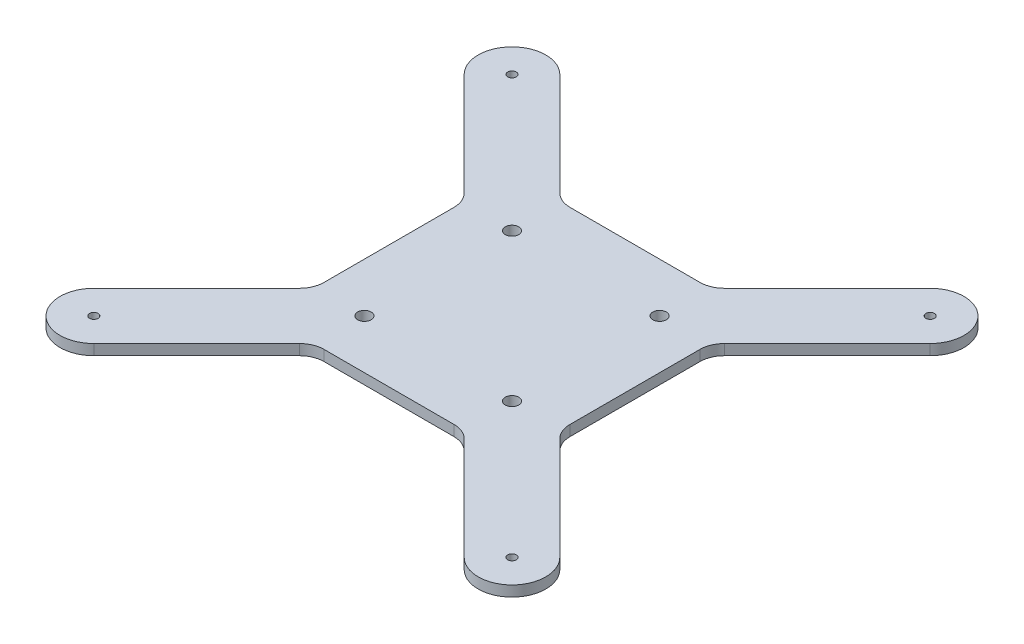
SolidWorks part; units mm, degrees
ref_plane "Front Plane" through (0, 0, 0) normal (0, 0, 1) x (1, 0, 0)
ref_plane "Top Plane" through (0, 0, 0) normal (0, 1, 0) x (1, 0, 0)
ref_plane "Right Plane" through (0, 0, 0) normal (1, 0, 0) x (0, 0, -1)
sketch "Sketch1" plane through (0, 0, 0) normal (0, 1, 0) x (1, 0, 0)
  line L0 (50, 100) -> (50, 0) construction
  line L1 (0, 0) -> (100, 0)
  line L2 (0, 0) -> (0, 100)
  line L3 (0, 100) -> (100, 100)
  line L4 (100, 0) -> (100, 100)
  line L5 (0, 50) -> (100, 50) construction
  circle A0 centre (20, 80) radius 2.75
  circle A1 centre (80, 80) radius 2.75
  circle A2 centre (80, 20) radius 2.75
  circle A3 centre (20, 20) radius 2.75
  circle A14 centre (50, 50) radius 7.5 construction
  point P54 (50, 50)
  dimension "D4" = 5.5
  dimension "D11" = 15
  dimension "D1" = 100
  dimension "D2" = 60
  dimension "D3" = 60
extrude "Boss-Extrude1" add sketch "Sketch1" along normal blind 4.3
sketch "Sketch2" plane through (0, 4.3, 0) normal (0, 1, 0) x (1, 0, 0)
  line L0 (50, 100) -> (50, 0) construction
  line L1 (100, 100) -> (0, 100) construction
  line L2 (0, 0) -> (100, 0) construction
  line L3 (0, 50) -> (100, 50) construction
  line L4 (0, 100) -> (0, 0) construction
  line L5 (100, 0) -> (100, 100) construction
  line L6 (0, 80.5546) -> (-44.7227, 125.2773)
  line L7 (-25.2773, 144.7227) -> (19.4454, 100)
  line L8 (0, 80.5546) -> (0, 100)
  line L9 (0, 100) -> (19.4454, 100)
  line L10 (100, 100) -> (100, 80.5546)
  line L11 (144.7227, 125.2773) -> (100, 80.5546)
  line L12 (80.5546, 100) -> (125.2773, 144.7227)
  line L13 (80.5546, 100) -> (100, 100)
  line L14 (100, 0) -> (80.5546, 0)
  line L15 (125.2773, -44.7227) -> (80.5546, 0)
  line L16 (100, 19.4454) -> (144.7227, -25.2773)
  line L17 (100, 19.4454) -> (100, 0)
  line L18 (0, 0) -> (0, 19.4454)
  line L19 (-44.7227, -25.2773) -> (0, 19.4454)
  line L20 (19.4454, 0) -> (-25.2773, -44.7227)
  line L21 (19.4454, 0) -> (0, 0)
  circle A0 centre (-35, 135) radius 1.75
  circle A1 centre (135, 135) radius 1.75
  circle A2 centre (135, -35) radius 1.75
  circle A3 centre (-35, -35) radius 1.75
  circle A4 centre (-35, 135) radius 13.75 construction
  circle A5 centre (135, 135) radius 13.75 construction
  circle A6 centre (135, -35) radius 13.75 construction
  circle A7 centre (-35, -35) radius 13.75 construction
  arc A8 (-44.7227, 125.2773) -> (-25.2773, 144.7227) centre (-35, 135) cw
  arc A9 (125.2773, 144.7227) -> (144.7227, 125.2773) centre (135, 135) cw
  arc A10 (144.7227, -25.2773) -> (125.2773, -44.7227) centre (135, -35) cw
  arc A11 (-25.2773, -44.7227) -> (-44.7227, -25.2773) centre (-35, -35) cw
  point P29 (50, 50)
  point P53 (50, 50)
  dimension "D3" = 3.5
  dimension "D4" = 12
  dimension "D1" = 170
  dimension "D2" = 170
  dimension "D5" = 45
  dimension "D6" = 45
  dimension "D7" = 4
extrude "Boss-Extrude2" add sketch "Sketch2" against normal up to surface (4.3 mm away) up to face at (80, 0, -17.25)
fillet "Fillet1" radius 10 8 edges at (0, 2.15, -19.4454) (19.4454, 2.15, 0) (80.5546, 2.15, 0) (100, 2.15, -19.4454) (100, 2.15, -80.5546) (80.5546, 2.15, -100) (19.4454, 2.15, -100) (0, 2.15, -80.5546)
